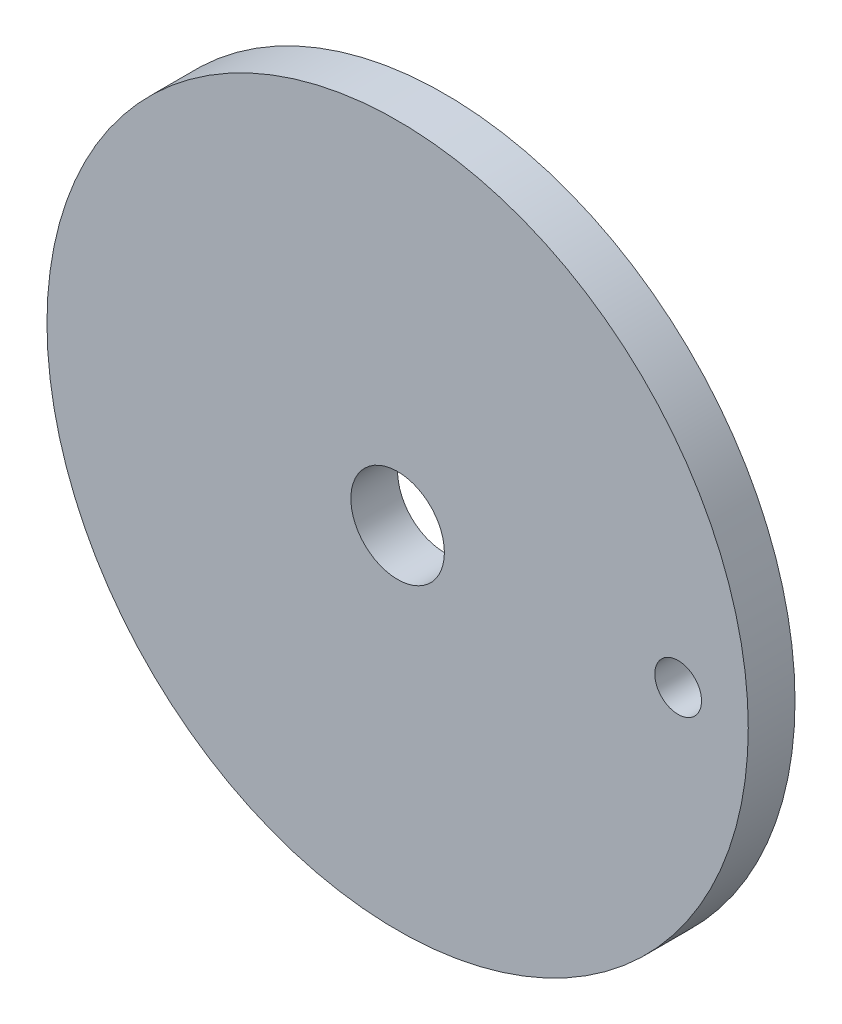
SolidWorks part; units mm, degrees
ref_plane "Front Plane" through (0, 0, 0) normal (0, 0, 1) x (1, 0, 0)
ref_plane "Top Plane" through (0, 0, 0) normal (0, 1, 0) x (1, 0, 0)
ref_plane "Right Plane" through (0, 0, 0) normal (1, 0, 0) x (0, 0, -1)
sketch "Sketch1" plane through (0, 0, 0) normal (0, 0, 1) x (1, 0, 0)
  circle A0 centre (0, 0) radius 1
  dimension "D1" = 2
extrude "Boss-Extrude1" add sketch "Sketch1" along normal blind 15
sketch "Sketch2" plane through (0, 0, 15) normal (0, 0, 1) x (1, 0, 0)
  circle A0 centre (0, 0) radius 7.5
  dimension "D1" = 15
extrude "Boss-Extrude2" add sketch "Sketch2" along normal blind 1
sketch "Sketch3" plane through (0, 0, 16) normal (0, 0, 1) x (1, 0, 0)
  line L0 (0, 0) -> (7.087, 0) construction
  circle A0 centre (6, 0) radius 0.5
  dimension "D1" = 1
  dimension "D2" = 6
sketch "Sketch4" plane through (0, 0, 16) normal (0, 0, 1) x (1, 0, 0)
  line L0 (0, 0) -> (6.0036, 0) construction
extrude "Cut-Extrude1" cut sketch "Sketch3" against normal blind 10
sketch "Sketch5" plane through (0, 0, 16) normal (0, 0, 1) x (1, 0, 0)
  circle A0 centre (0, 0) radius 1
  dimension "D1" = 2
extrude "Cut-Extrude2" cut sketch "Sketch5" against normal blind 20
